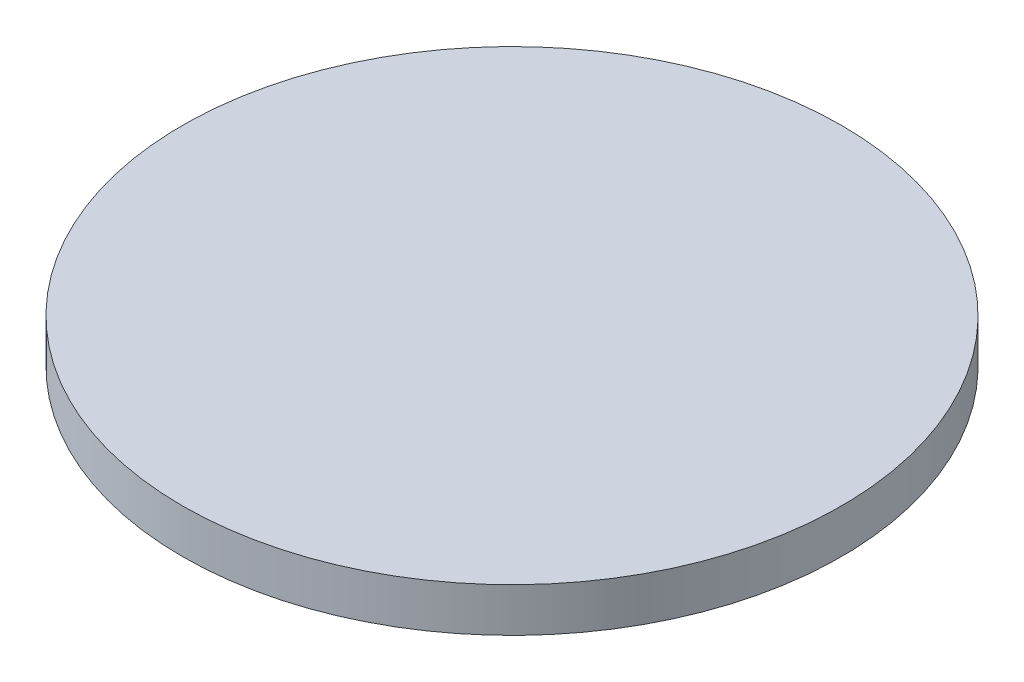
SolidWorks part; units mm, degrees
ref_plane "Plan de face" through (0, 0, 0) normal (0, 0, 1) x (1, 0, 0)
ref_plane "Plan de dessus" through (0, 0, 0) normal (0, 1, 0) x (1, 0, 0)
ref_plane "Plan de droite" through (0, 0, 0) normal (1, 0, 0) x (0, 0, -1)
sketch "Esquisse1" plane through (0, 0, 0) normal (0, 1, 0) x (1, 0, 0)
  circle A0 centre (0, 0) radius 75
  dimension "D1" = 150
extrude "Boss.-Extru.1" add sketch "Esquisse1" along normal blind 10
